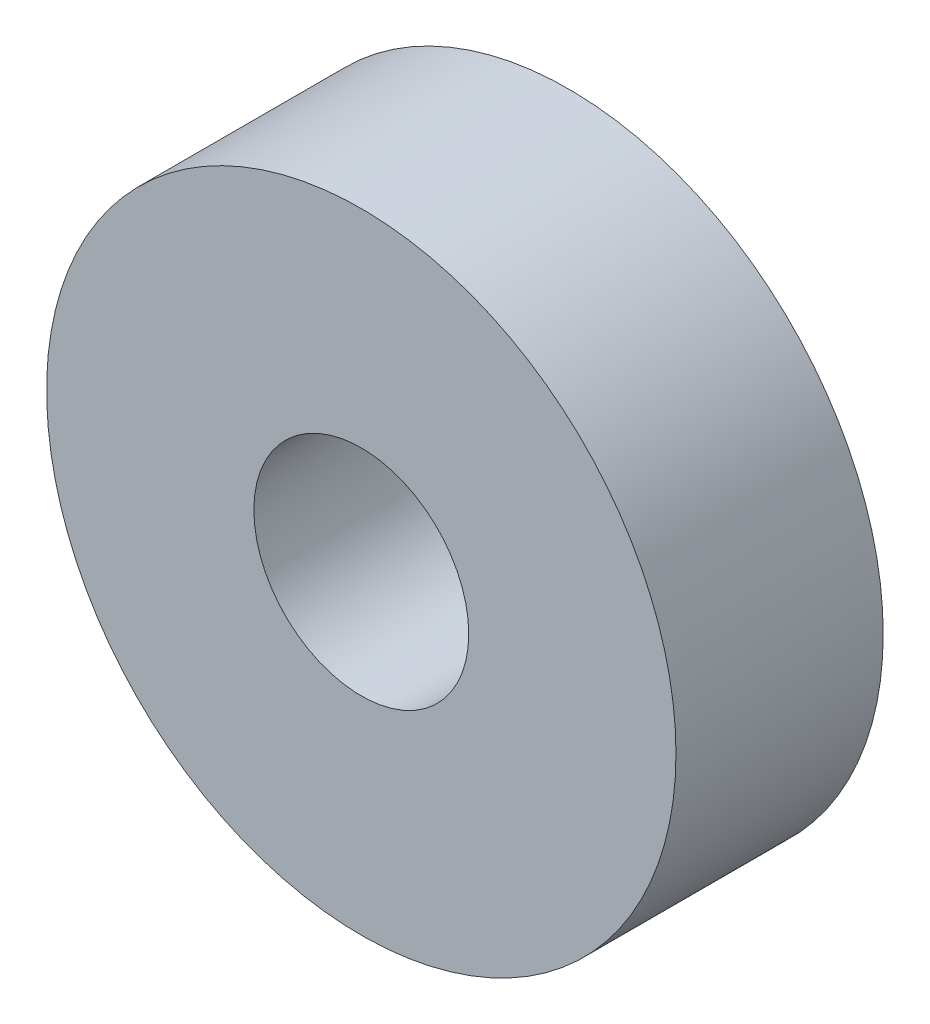
SolidWorks part; units mm, degrees
ref_plane "Front Plane" through (0, 0, 0) normal (0, 0, 1) x (1, 0, 0)
ref_plane "Top Plane" through (0, 0, 0) normal (0, 1, 0) x (1, 0, 0)
ref_plane "Right Plane" through (0, 0, 0) normal (1, 0, 0) x (0, 0, -1)
sketch "Sketch2" plane through (0, 0, 0) normal (0, 0, 1) x (1, 0, 0)
  circle A0 centre (0, 0) radius 41
  dimension "D1" = 82
extrude "Boss-Extrude1" add sketch "Sketch2" against normal blind 27
sketch "Sketch3" plane through (0, 0, 0) normal (0, 0, 1) x (1, 0, 0)
  circle A0 centre (0, 0) radius 14
  dimension "D1" = 28
extrude "Cut-Extrude1" cut sketch "Sketch3" against normal blind 27
